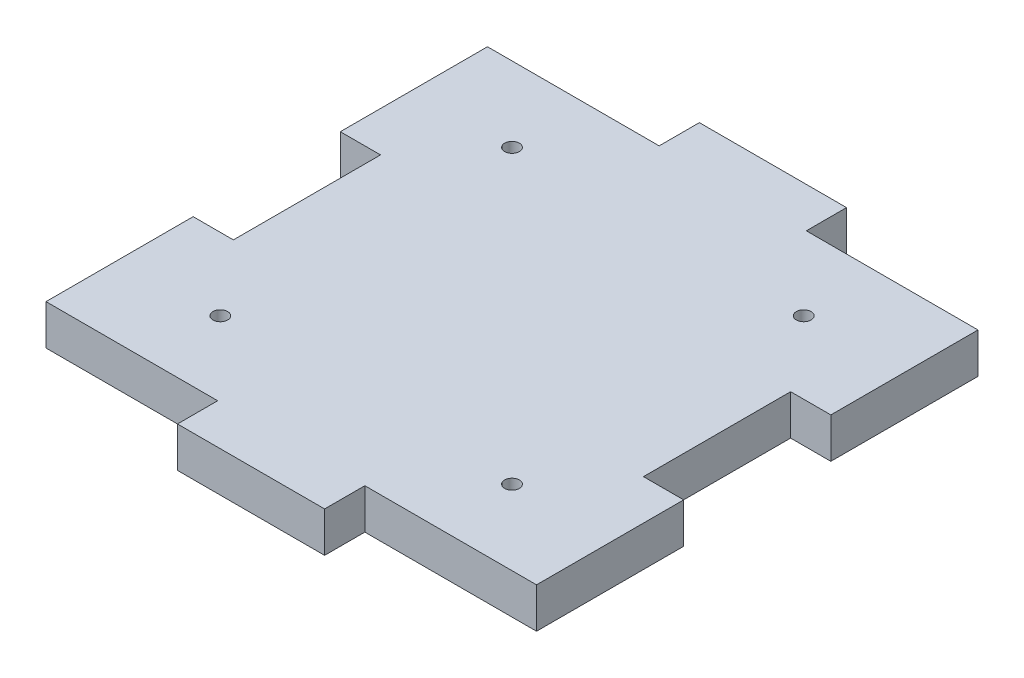
SolidWorks part; units mm, degrees
material "Corrugated Paper"
ref_plane "Front Plane" through (0, 0, 0) normal (0, 0, 1) x (1, 0, 0)
ref_plane "Top Plane" through (0, 0, 0) normal (0, 1, 0) x (1, 0, 0)
ref_plane "Right Plane" through (0, 0, 0) normal (1, 0, 0) x (0, 0, -1)
sketch "Sketch1" plane through (0, 0, 0) normal (0, 1, 0) x (1, 0, 0)
  line L0 (0, 15) -> (4.1, 15)
  line L1 (0, 0) -> (0, 15)
  line L2 (0, 22.5) -> (50, 22.5) construction
  line L3 (4.1, 15) -> (4.1, 30)
  line L4 (4.1, 30) -> (0, 30)
  line L5 (0, 30) -> (0, 45)
  line L6 (0, 45) -> (50, 45) construction
  line L7 (50, 45) -> (50, 30)
  line L8 (50, 30) -> (45.9, 30)
  line L9 (45.9, 30) -> (45.9, 15)
  line L10 (45.9, 15) -> (50, 15)
  line L11 (50, 15) -> (50, 0)
  line L12 (50, 0) -> (32.5, 0)
  line L13 (32.5, 0) -> (32.5, -4.1)
  line L14 (32.5, -4.1) -> (17.5, -4.1)
  line L15 (17.5, -4.1) -> (17.5, 0)
  line L16 (17.5, 0) -> (0, 0)
  line L17 (0, 45) -> (0, 0) construction
  line L18 (0, 0) -> (50, 0) construction
  line L19 (32.5, 45) -> (32.5, 49.1)
  line L20 (50, 45) -> (32.5, 45)
  line L21 (17.5, 49.1) -> (17.5, 45)
  line L22 (32.5, 49.1) -> (17.5, 49.1)
  line L23 (17.5, 45) -> (0, 45)
  line L24 (25, 49.1) -> (25, -4.1) construction
  line L26 (10.1331, 7.6331) -> (39.8669, 7.6331) construction
  line L27 (10.1331, 7.6331) -> (10.1331, 37.3669) construction
  line L28 (10.1331, 37.3669) -> (39.8669, 37.3669) construction
  line L29 (39.8669, 7.6331) -> (39.8669, 37.3669) construction
  line L30 (10.1331, 7.6331) -> (39.8669, 37.3669) construction
  line L31 (10.1331, 37.3669) -> (39.8669, 7.6331) construction
  circle A0 centre (10.1331, 7.6331) radius 0.75
  circle A1 centre (10.1331, 37.3669) radius 0.75
  circle A2 centre (39.8669, 37.3669) radius 0.75
  circle A3 centre (39.8669, 7.6331) radius 0.75
  point P25 (25, 22.5)
  dimension "D7" = 1.5
  dimension "D1" = 45
  dimension "D2" = 50
  dimension "D3" = 4.1
  dimension "D4" = 15
  dimension "D6" = 42.05
extrude "Boss-Extrude1" add sketch "Sketch1" along normal blind 4.1
